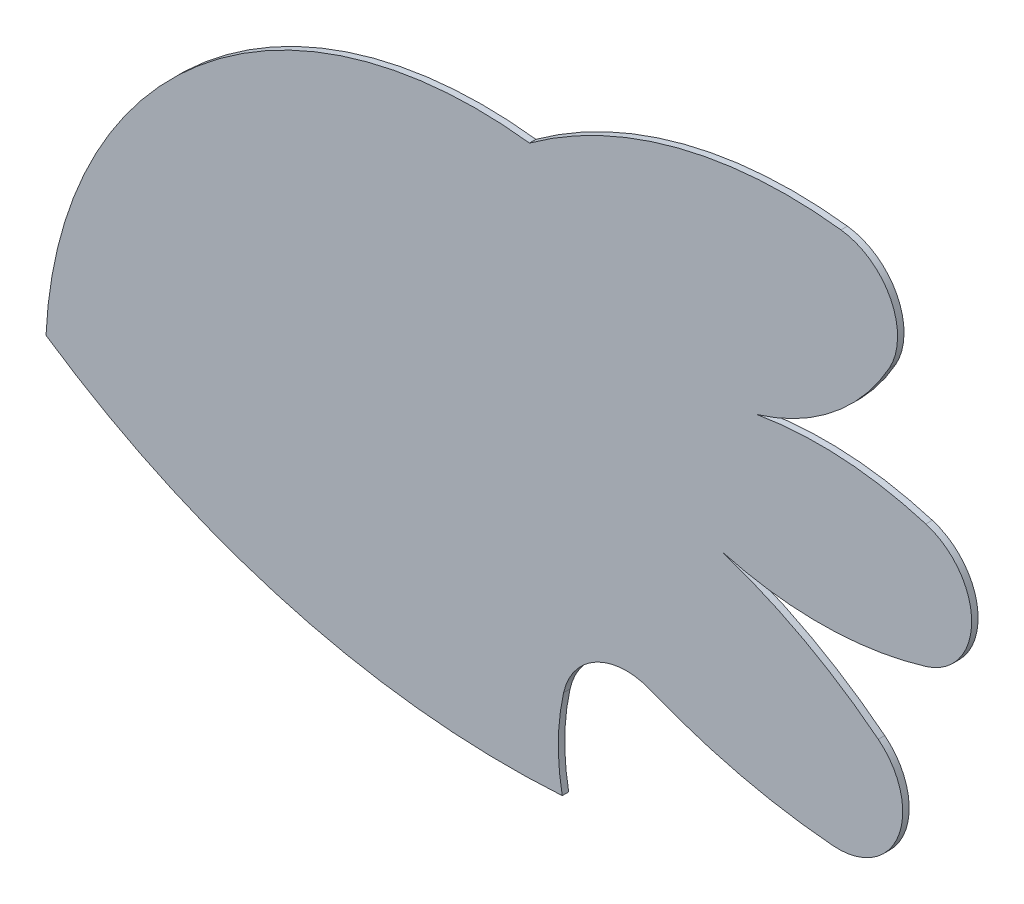
SolidWorks part; units mm, degrees
ref_plane "Alzado" through (0, 0, 0) normal (0, 0, 1) x (1, 0, 0)
ref_plane "Planta" through (0, 0, 0) normal (0, 1, 0) x (1, 0, 0)
ref_plane "Vista lateral" through (0, 0, 0) normal (1, 0, 0) x (0, 0, -1)
sketch "Model" plane through (0, 0, 0) normal (0, 0, 1) x (1, 0, 0)
  arc A0 (22.5402, 13.8549) -> (30.5484, 11.6753) centre (29.7151, 24.4151) ccw
  arc A1 (36.189, 16.2312) -> (36.189, 18.1457) centre (35.8998, 17.1884) ccw
  arc A2 (33.0402, 16.1884) -> (36.189, 16.2312) centre (34.5402, 21.6884) ccw
  arc A3 (35.4513, 14.8837) -> (33.0402, 16.1884) centre (30.5402, 8.6884) ccw
  arc A4 (34.7477, 13.1035) -> (35.4513, 14.8837) centre (34.8301, 14.1001) ccw
  arc A5 (31.9217, 13.7775) -> (34.7477, 13.1035) centre (35.5402, 22.6884) ccw
  arc A6 (33.5697, 18.3061) -> (35.6219, 19.9554) centre (32.5402, 21.6884) ccw
  arc A7 (31.9217, 13.7775) -> (30.5695, 13.0692) centre (31.5454, 12.8509) ccw
  arc A8 (30.5695, 13.0692) -> (30.5484, 11.6753) centre (33.9137, 12.3213) ccw
  arc A9 (36.189, 18.1457) -> (33.5697, 18.3061) centre (34.5402, 12.6884) ccw
  arc A10 (30.0402, 20.1884) -> (22.5402, 13.8549) centre (29.2208, 13.5514) ccw
  arc A11 (34.8727, 21.438) -> (30.0402, 20.1884) centre (34.0402, 14.6884) ccw
  arc A12 (35.6219, 19.9554) -> (34.8727, 21.438) centre (34.7503, 20.4456) ccw
extrude "Saliente-Extruir1" add sketch "Model" along normal blind 0.1
